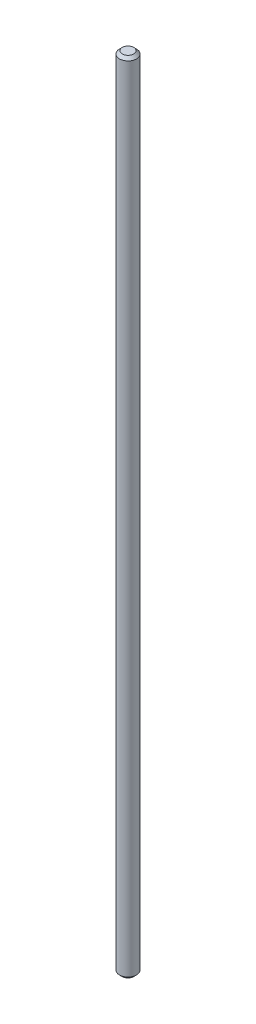
SolidWorks part; units mm, degrees
material "Acero inoxidable al cromo"
ref_plane "Front" through (0, 0, 0) normal (0, 0, 1) x (1, 0, 0)
ref_plane "Top" through (0, 0, 0) normal (0, 1, 0) x (1, 0, 0)
ref_plane "Right" through (0, 0, 0) normal (1, 0, 0) x (0, 0, -1)
sketch "Croquis1" plane through (0, 0, 0) normal (0, 1, 0) x (1, 0, 0)
  circle A0 centre (0, 0) radius 1.5
  dimension "D1" = 3
extrude "Saliente-Extruir1" add sketch "Croquis1" along normal blind 140
chamfer "Chaflán1" distance 0.5 angle 45 2 edges at (0, 140, 1.5) (0, 0, 1.5)
